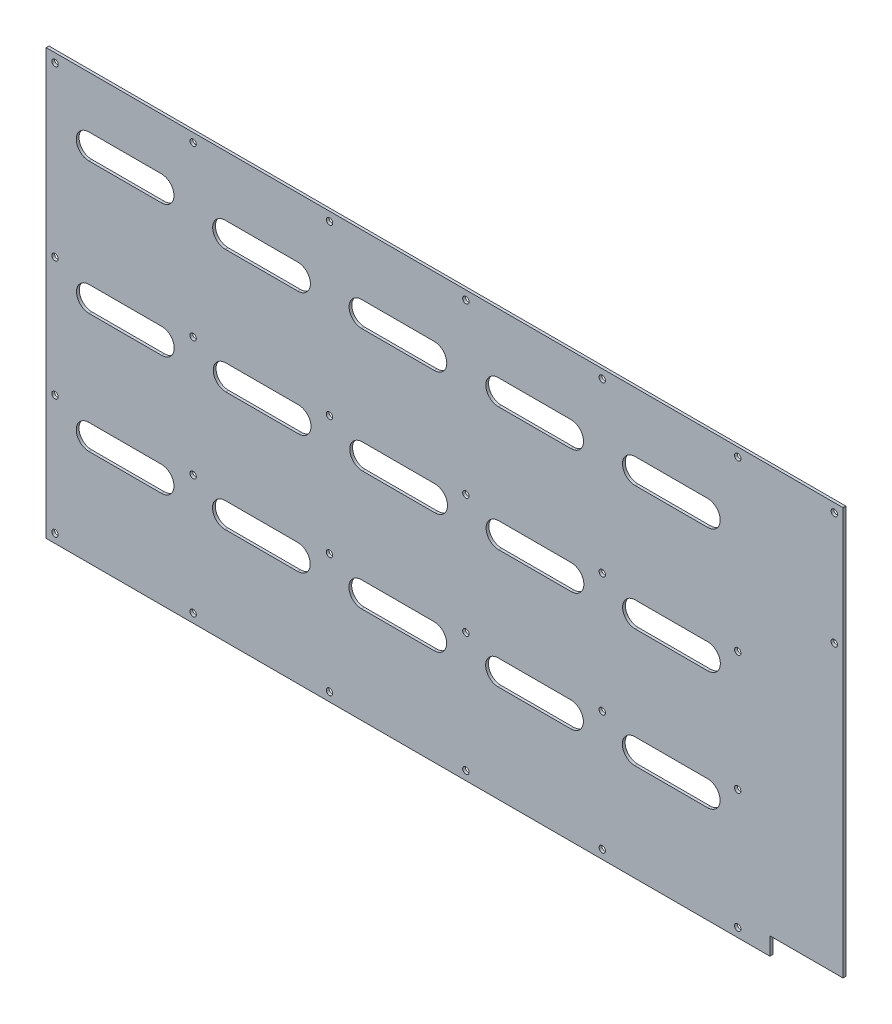
SolidWorks part; units mm, degrees
ref_plane "Front Plane" through (0, 0, 0) normal (0, 0, 1) x (1, 0, 0)
ref_plane "Top Plane" through (0, 0, 0) normal (0, 1, 0) x (1, 0, 0)
ref_plane "Right Plane" through (0, 0, 0) normal (1, 0, 0) x (0, 0, -1)
sketch "Model" plane through (0, 0, 0) normal (0, 0, 1) x (1, 0, 0)
  line L0 (0, 0) -> (415.29, 0)
  line L1 (415.29, 0) -> (415.29, 10.16)
  line L2 (415.29, 10.16) -> (457.2, 10.16)
  line L3 (457.2, 10.16) -> (457.2, 243.84)
  line L4 (457.2, 243.84) -> (0, 243.84)
  line L5 (0, 243.84) -> (0, 0)
  line L6 (24.4986, 214.1733) -> (66.1546, 214.1733)
  line L7 (66.1546, 199.7717) -> (24.4986, 199.7717)
  line L8 (102.7478, 209.4238) -> (144.4038, 209.4238)
  line L9 (144.4038, 195.0222) -> (102.7478, 195.0222)
  line L10 (180.9835, 209.1621) -> (222.6395, 209.1621)
  line L11 (222.6395, 194.7605) -> (180.9835, 194.7605)
  line L12 (259.428, 209.5421) -> (301.084, 209.5421)
  line L13 (301.084, 195.1405) -> (259.428, 195.1405)
  line L14 (337.8398, 209.595) -> (379.4958, 209.595)
  line L15 (379.4958, 195.1933) -> (337.8398, 195.1933)
  line L16 (24.6392, 138.4629) -> (66.2952, 138.4629)
  line L17 (66.2952, 124.0613) -> (24.6392, 124.0613)
  line L18 (103.0965, 138.71) -> (144.7525, 138.71)
  line L19 (144.7525, 124.3084) -> (103.0965, 124.3084)
  line L20 (181.3907, 138.6208) -> (223.0467, 138.6208)
  line L21 (223.0467, 124.2191) -> (181.3907, 124.2191)
  line L22 (259.6081, 138.5703) -> (301.2641, 138.5703)
  line L23 (301.2641, 124.1687) -> (259.6081, 124.1687)
  line L24 (337.9084, 138.3784) -> (379.5644, 138.3784)
  line L25 (379.5644, 123.9768) -> (337.9084, 123.9768)
  line L26 (24.487, 69.8646) -> (66.143, 69.8646)
  line L27 (66.143, 55.463) -> (24.487, 55.463)
  line L28 (102.6591, 70.1547) -> (144.3151, 70.1547)
  line L29 (144.3151, 55.7531) -> (102.6591, 55.7531)
  line L30 (180.8949, 69.893) -> (222.5509, 69.893)
  line L31 (222.5509, 55.4913) -> (180.8949, 55.4913)
  line L32 (259.3394, 70.2729) -> (300.9954, 70.2729)
  line L33 (300.9954, 55.8713) -> (259.3394, 55.8713)
  line L34 (337.7512, 70.3258) -> (379.4072, 70.3258)
  line L35 (379.4072, 55.9242) -> (337.7512, 55.9242)
  line L276 (452.12, 173.736) -> (452.12, 174.244)
  line L277 (451.866, 173.99) -> (452.374, 173.99)
  line L278 (452.12, 173.736) -> (452.12, 174.244)
  line L279 (451.866, 173.99) -> (452.374, 173.99)
  line L280 (452.12, 173.736) -> (452.12, 174.244)
  line L281 (451.866, 173.99) -> (452.374, 173.99)
  line L282 (452.12, 173.736) -> (452.12, 174.244)
  line L283 (451.866, 173.99) -> (452.374, 173.99)
  line L284 (452.12, 173.736) -> (452.12, 174.244)
  line L285 (451.866, 173.99) -> (452.374, 173.99)
  line L286 (452.12, 173.736) -> (452.12, 174.244)
  line L287 (451.866, 173.99) -> (452.374, 173.99)
  line L288 (452.12, 173.736) -> (452.12, 174.244)
  line L289 (451.866, 173.99) -> (452.374, 173.99)
  line L290 (452.12, 173.736) -> (452.12, 174.244)
  line L291 (451.866, 173.99) -> (452.374, 173.99)
  line L292 (452.12, 238.506) -> (452.12, 239.014)
  line L293 (451.866, 238.76) -> (452.374, 238.76)
  line L294 (452.12, 238.506) -> (452.12, 239.014)
  line L295 (451.866, 238.76) -> (452.374, 238.76)
  line L296 (452.12, 238.506) -> (452.12, 239.014)
  line L297 (451.866, 238.76) -> (452.374, 238.76)
  line L298 (452.12, 238.506) -> (452.12, 239.014)
  line L299 (451.866, 238.76) -> (452.374, 238.76)
  line L300 (452.12, 238.506) -> (452.12, 239.014)
  line L301 (451.866, 238.76) -> (452.374, 238.76)
  line L302 (452.12, 238.506) -> (452.12, 239.014)
  line L303 (451.866, 238.76) -> (452.374, 238.76)
  line L304 (452.12, 238.506) -> (452.12, 239.014)
  line L305 (451.866, 238.76) -> (452.374, 238.76)
  line L306 (452.12, 238.506) -> (452.12, 239.014)
  line L307 (451.866, 238.76) -> (452.374, 238.76)
  line L308 (5.08, 4.826) -> (5.08, 5.334)
  line L309 (4.826, 5.08) -> (5.334, 5.08)
  line L310 (5.08, 4.826) -> (5.08, 5.334)
  line L311 (4.826, 5.08) -> (5.334, 5.08)
  line L312 (5.08, 4.826) -> (5.08, 5.334)
  line L313 (4.826, 5.08) -> (5.334, 5.08)
  line L314 (5.08, 4.826) -> (5.08, 5.334)
  line L315 (4.826, 5.08) -> (5.334, 5.08)
  line L316 (5.08, 4.826) -> (5.08, 5.334)
  line L317 (4.826, 5.08) -> (5.334, 5.08)
  line L318 (5.08, 4.826) -> (5.08, 5.334)
  line L319 (4.826, 5.08) -> (5.334, 5.08)
  line L320 (5.08, 4.826) -> (5.08, 5.334)
  line L321 (4.826, 5.08) -> (5.334, 5.08)
  line L322 (5.08, 4.826) -> (5.08, 5.334)
  line L323 (4.826, 5.08) -> (5.334, 5.08)
  line L324 (5.08, 73.406) -> (5.08, 73.914)
  line L325 (4.826, 73.66) -> (5.334, 73.66)
  line L326 (5.08, 73.406) -> (5.08, 73.914)
  line L327 (4.826, 73.66) -> (5.334, 73.66)
  line L328 (5.08, 73.406) -> (5.08, 73.914)
  line L329 (4.826, 73.66) -> (5.334, 73.66)
  line L330 (5.08, 73.406) -> (5.08, 73.914)
  line L331 (4.826, 73.66) -> (5.334, 73.66)
  line L332 (5.08, 73.406) -> (5.08, 73.914)
  line L333 (4.826, 73.66) -> (5.334, 73.66)
  line L334 (5.08, 73.406) -> (5.08, 73.914)
  line L335 (4.826, 73.66) -> (5.334, 73.66)
  line L336 (5.08, 73.406) -> (5.08, 73.914)
  line L337 (4.826, 73.66) -> (5.334, 73.66)
  line L338 (5.08, 73.406) -> (5.08, 73.914)
  line L339 (4.826, 73.66) -> (5.334, 73.66)
  line L340 (5.08, 141.986) -> (5.08, 142.494)
  line L341 (4.826, 142.24) -> (5.334, 142.24)
  line L342 (5.08, 141.986) -> (5.08, 142.494)
  line L343 (4.826, 142.24) -> (5.334, 142.24)
  line L344 (5.08, 141.986) -> (5.08, 142.494)
  line L345 (4.826, 142.24) -> (5.334, 142.24)
  line L346 (5.08, 141.986) -> (5.08, 142.494)
  line L347 (4.826, 142.24) -> (5.334, 142.24)
  line L348 (5.08, 141.986) -> (5.08, 142.494)
  line L349 (4.826, 142.24) -> (5.334, 142.24)
  line L350 (5.08, 141.986) -> (5.08, 142.494)
  line L351 (4.826, 142.24) -> (5.334, 142.24)
  line L352 (5.08, 141.986) -> (5.08, 142.494)
  line L353 (4.826, 142.24) -> (5.334, 142.24)
  line L354 (5.08, 141.986) -> (5.08, 142.494)
  line L355 (4.826, 142.24) -> (5.334, 142.24)
  line L356 (5.08, 238.506) -> (5.08, 239.014)
  line L357 (4.826, 238.76) -> (5.334, 238.76)
  line L358 (5.08, 238.506) -> (5.08, 239.014)
  line L359 (4.826, 238.76) -> (5.334, 238.76)
  line L360 (5.08, 238.506) -> (5.08, 239.014)
  line L361 (4.826, 238.76) -> (5.334, 238.76)
  line L362 (5.08, 238.506) -> (5.08, 239.014)
  line L363 (4.826, 238.76) -> (5.334, 238.76)
  line L364 (5.08, 238.506) -> (5.08, 239.014)
  line L365 (4.826, 238.76) -> (5.334, 238.76)
  line L366 (5.08, 238.506) -> (5.08, 239.014)
  line L367 (4.826, 238.76) -> (5.334, 238.76)
  line L368 (5.08, 238.506) -> (5.08, 239.014)
  line L369 (4.826, 238.76) -> (5.334, 238.76)
  line L370 (5.08, 238.506) -> (5.08, 239.014)
  line L371 (4.826, 238.76) -> (5.334, 238.76)
  line L372 (84.328, 4.826) -> (84.328, 5.334)
  line L373 (84.074, 5.08) -> (84.582, 5.08)
  line L374 (84.328, 4.826) -> (84.328, 5.334)
  line L375 (84.074, 5.08) -> (84.582, 5.08)
  line L376 (84.328, 4.826) -> (84.328, 5.334)
  line L377 (84.074, 5.08) -> (84.582, 5.08)
  line L378 (84.328, 4.826) -> (84.328, 5.334)
  line L379 (84.074, 5.08) -> (84.582, 5.08)
  line L380 (84.328, 4.826) -> (84.328, 5.334)
  line L381 (84.074, 5.08) -> (84.582, 5.08)
  line L382 (84.328, 4.826) -> (84.328, 5.334)
  line L383 (84.074, 5.08) -> (84.582, 5.08)
  line L384 (84.328, 4.826) -> (84.328, 5.334)
  line L385 (84.074, 5.08) -> (84.582, 5.08)
  line L386 (84.328, 4.826) -> (84.328, 5.334)
  line L387 (84.074, 5.08) -> (84.582, 5.08)
  line L388 (84.328, 73.406) -> (84.328, 73.914)
  line L389 (84.074, 73.66) -> (84.582, 73.66)
  line L390 (84.328, 73.406) -> (84.328, 73.914)
  line L391 (84.074, 73.66) -> (84.582, 73.66)
  line L392 (84.328, 73.406) -> (84.328, 73.914)
  line L393 (84.074, 73.66) -> (84.582, 73.66)
  line L394 (84.328, 73.406) -> (84.328, 73.914)
  line L395 (84.074, 73.66) -> (84.582, 73.66)
  line L396 (84.328, 73.406) -> (84.328, 73.914)
  line L397 (84.074, 73.66) -> (84.582, 73.66)
  line L398 (84.328, 73.406) -> (84.328, 73.914)
  line L399 (84.074, 73.66) -> (84.582, 73.66)
  line L400 (84.328, 73.406) -> (84.328, 73.914)
  line L401 (84.074, 73.66) -> (84.582, 73.66)
  line L402 (84.328, 73.406) -> (84.328, 73.914)
  line L403 (84.074, 73.66) -> (84.582, 73.66)
  line L404 (84.328, 141.986) -> (84.328, 142.494)
  line L405 (84.074, 142.24) -> (84.582, 142.24)
  line L406 (84.328, 141.986) -> (84.328, 142.494)
  line L407 (84.074, 142.24) -> (84.582, 142.24)
  line L408 (84.328, 141.986) -> (84.328, 142.494)
  line L409 (84.074, 142.24) -> (84.582, 142.24)
  line L410 (84.328, 141.986) -> (84.328, 142.494)
  line L411 (84.074, 142.24) -> (84.582, 142.24)
  line L412 (84.328, 141.986) -> (84.328, 142.494)
  line L413 (84.074, 142.24) -> (84.582, 142.24)
  line L414 (84.328, 141.986) -> (84.328, 142.494)
  line L415 (84.074, 142.24) -> (84.582, 142.24)
  line L416 (84.328, 141.986) -> (84.328, 142.494)
  line L417 (84.074, 142.24) -> (84.582, 142.24)
  line L418 (84.328, 141.986) -> (84.328, 142.494)
  line L419 (84.074, 142.24) -> (84.582, 142.24)
  line L420 (84.328, 238.506) -> (84.328, 239.014)
  line L421 (84.074, 238.76) -> (84.582, 238.76)
  line L422 (84.328, 238.506) -> (84.328, 239.014)
  line L423 (84.074, 238.76) -> (84.582, 238.76)
  line L424 (84.328, 238.506) -> (84.328, 239.014)
  line L425 (84.074, 238.76) -> (84.582, 238.76)
  line L426 (84.328, 238.506) -> (84.328, 239.014)
  line L427 (84.074, 238.76) -> (84.582, 238.76)
  line L428 (84.328, 238.506) -> (84.328, 239.014)
  line L429 (84.074, 238.76) -> (84.582, 238.76)
  line L430 (84.328, 238.506) -> (84.328, 239.014)
  line L431 (84.074, 238.76) -> (84.582, 238.76)
  line L432 (84.328, 238.506) -> (84.328, 239.014)
  line L433 (84.074, 238.76) -> (84.582, 238.76)
  line L434 (84.328, 238.506) -> (84.328, 239.014)
  line L435 (84.074, 238.76) -> (84.582, 238.76)
  line L436 (162.56, 4.826) -> (162.56, 5.334)
  line L437 (162.306, 5.08) -> (162.814, 5.08)
  line L438 (162.56, 4.826) -> (162.56, 5.334)
  line L439 (162.306, 5.08) -> (162.814, 5.08)
  line L440 (162.56, 4.826) -> (162.56, 5.334)
  line L441 (162.306, 5.08) -> (162.814, 5.08)
  line L442 (162.56, 4.826) -> (162.56, 5.334)
  line L443 (162.306, 5.08) -> (162.814, 5.08)
  line L444 (162.56, 4.826) -> (162.56, 5.334)
  line L445 (162.306, 5.08) -> (162.814, 5.08)
  line L446 (162.56, 4.826) -> (162.56, 5.334)
  line L447 (162.306, 5.08) -> (162.814, 5.08)
  line L448 (162.56, 4.826) -> (162.56, 5.334)
  line L449 (162.306, 5.08) -> (162.814, 5.08)
  line L450 (162.56, 4.826) -> (162.56, 5.334)
  line L451 (162.306, 5.08) -> (162.814, 5.08)
  line L452 (162.56, 73.406) -> (162.56, 73.914)
  line L453 (162.306, 73.66) -> (162.814, 73.66)
  line L454 (162.56, 73.406) -> (162.56, 73.914)
  line L455 (162.306, 73.66) -> (162.814, 73.66)
  line L456 (162.56, 73.406) -> (162.56, 73.914)
  line L457 (162.306, 73.66) -> (162.814, 73.66)
  line L458 (162.56, 73.406) -> (162.56, 73.914)
  line L459 (162.306, 73.66) -> (162.814, 73.66)
  line L460 (162.56, 73.406) -> (162.56, 73.914)
  line L461 (162.306, 73.66) -> (162.814, 73.66)
  line L462 (162.56, 73.406) -> (162.56, 73.914)
  line L463 (162.306, 73.66) -> (162.814, 73.66)
  line L464 (162.56, 73.406) -> (162.56, 73.914)
  line L465 (162.306, 73.66) -> (162.814, 73.66)
  line L466 (162.56, 73.406) -> (162.56, 73.914)
  line L467 (162.306, 73.66) -> (162.814, 73.66)
  line L468 (162.56, 141.986) -> (162.56, 142.494)
  line L469 (162.306, 142.24) -> (162.814, 142.24)
  line L470 (162.56, 141.986) -> (162.56, 142.494)
  line L471 (162.306, 142.24) -> (162.814, 142.24)
  line L472 (162.56, 141.986) -> (162.56, 142.494)
  line L473 (162.306, 142.24) -> (162.814, 142.24)
  line L474 (162.56, 141.986) -> (162.56, 142.494)
  line L475 (162.306, 142.24) -> (162.814, 142.24)
  line L476 (162.56, 141.986) -> (162.56, 142.494)
  line L477 (162.306, 142.24) -> (162.814, 142.24)
  line L478 (162.56, 141.986) -> (162.56, 142.494)
  line L479 (162.306, 142.24) -> (162.814, 142.24)
  line L480 (162.56, 141.986) -> (162.56, 142.494)
  line L481 (162.306, 142.24) -> (162.814, 142.24)
  line L482 (162.56, 141.986) -> (162.56, 142.494)
  line L483 (162.306, 142.24) -> (162.814, 142.24)
  line L484 (162.56, 238.506) -> (162.56, 239.014)
  line L485 (162.306, 238.76) -> (162.814, 238.76)
  line L486 (162.56, 238.506) -> (162.56, 239.014)
  line L487 (162.306, 238.76) -> (162.814, 238.76)
  line L488 (162.56, 238.506) -> (162.56, 239.014)
  line L489 (162.306, 238.76) -> (162.814, 238.76)
  line L490 (162.56, 238.506) -> (162.56, 239.014)
  line L491 (162.306, 238.76) -> (162.814, 238.76)
  line L492 (162.56, 238.506) -> (162.56, 239.014)
  line L493 (162.306, 238.76) -> (162.814, 238.76)
  line L494 (162.56, 238.506) -> (162.56, 239.014)
  line L495 (162.306, 238.76) -> (162.814, 238.76)
  line L496 (162.56, 238.506) -> (162.56, 239.014)
  line L497 (162.306, 238.76) -> (162.814, 238.76)
  line L498 (162.56, 238.506) -> (162.56, 239.014)
  line L499 (162.306, 238.76) -> (162.814, 238.76)
  line L500 (240.7699, 4.827) -> (240.8141, 5.333)
  line L501 (240.539, 5.1021) -> (241.045, 5.0579)
  line L502 (240.7699, 4.827) -> (240.8141, 5.333)
  line L503 (240.539, 5.1021) -> (241.045, 5.0579)
  line L504 (240.7699, 4.827) -> (240.8141, 5.333)
  line L505 (240.539, 5.1021) -> (241.045, 5.0579)
  line L506 (240.7699, 4.827) -> (240.8141, 5.333)
  line L507 (240.539, 5.1021) -> (241.045, 5.0579)
  line L508 (240.7699, 4.827) -> (240.8141, 5.333)
  line L509 (240.539, 5.1021) -> (241.045, 5.0579)
  line L510 (240.7699, 4.827) -> (240.8141, 5.333)
  line L511 (240.539, 5.1021) -> (241.045, 5.0579)
  line L512 (240.7699, 4.827) -> (240.8141, 5.333)
  line L513 (240.539, 5.1021) -> (241.045, 5.0579)
  line L514 (240.7699, 4.827) -> (240.8141, 5.333)
  line L515 (240.539, 5.1021) -> (241.045, 5.0579)
  line L516 (240.792, 73.406) -> (240.792, 73.914)
  line L517 (240.538, 73.66) -> (241.046, 73.66)
  line L518 (240.792, 73.406) -> (240.792, 73.914)
  line L519 (240.538, 73.66) -> (241.046, 73.66)
  line L520 (240.792, 73.406) -> (240.792, 73.914)
  line L521 (240.538, 73.66) -> (241.046, 73.66)
  line L522 (240.792, 73.406) -> (240.792, 73.914)
  line L523 (240.538, 73.66) -> (241.046, 73.66)
  line L524 (240.792, 73.406) -> (240.792, 73.914)
  line L525 (240.538, 73.66) -> (241.046, 73.66)
  line L526 (240.792, 73.406) -> (240.792, 73.914)
  line L527 (240.538, 73.66) -> (241.046, 73.66)
  line L528 (240.792, 73.406) -> (240.792, 73.914)
  line L529 (240.538, 73.66) -> (241.046, 73.66)
  line L530 (240.792, 73.406) -> (240.792, 73.914)
  line L531 (240.538, 73.66) -> (241.046, 73.66)
  line L532 (240.792, 141.986) -> (240.792, 142.494)
  line L533 (240.538, 142.24) -> (241.046, 142.24)
  line L534 (240.792, 141.986) -> (240.792, 142.494)
  line L535 (240.538, 142.24) -> (241.046, 142.24)
  line L536 (240.792, 141.986) -> (240.792, 142.494)
  line L537 (240.538, 142.24) -> (241.046, 142.24)
  line L538 (240.792, 141.986) -> (240.792, 142.494)
  line L539 (240.538, 142.24) -> (241.046, 142.24)
  line L540 (240.792, 141.986) -> (240.792, 142.494)
  line L541 (240.538, 142.24) -> (241.046, 142.24)
  line L542 (240.792, 141.986) -> (240.792, 142.494)
  line L543 (240.538, 142.24) -> (241.046, 142.24)
  line L544 (240.792, 141.986) -> (240.792, 142.494)
  line L545 (240.538, 142.24) -> (241.046, 142.24)
  line L546 (240.792, 141.986) -> (240.792, 142.494)
  line L547 (240.538, 142.24) -> (241.046, 142.24)
  line L548 (240.792, 238.506) -> (240.792, 239.014)
  line L549 (240.538, 238.76) -> (241.046, 238.76)
  line L550 (240.792, 238.506) -> (240.792, 239.014)
  line L551 (240.538, 238.76) -> (241.046, 238.76)
  line L552 (240.792, 238.506) -> (240.792, 239.014)
  line L553 (240.538, 238.76) -> (241.046, 238.76)
  line L554 (240.792, 238.506) -> (240.792, 239.014)
  line L555 (240.538, 238.76) -> (241.046, 238.76)
  line L556 (240.792, 238.506) -> (240.792, 239.014)
  line L557 (240.538, 238.76) -> (241.046, 238.76)
  line L558 (240.792, 238.506) -> (240.792, 239.014)
  line L559 (240.538, 238.76) -> (241.046, 238.76)
  line L560 (240.792, 238.506) -> (240.792, 239.014)
  line L561 (240.538, 238.76) -> (241.046, 238.76)
  line L562 (240.792, 238.506) -> (240.792, 239.014)
  line L563 (240.538, 238.76) -> (241.046, 238.76)
  line L564 (319.024, 4.826) -> (319.024, 5.334)
  line L565 (318.77, 5.08) -> (319.278, 5.08)
  line L566 (319.024, 4.826) -> (319.024, 5.334)
  line L567 (318.77, 5.08) -> (319.278, 5.08)
  line L568 (319.024, 4.826) -> (319.024, 5.334)
  line L569 (318.77, 5.08) -> (319.278, 5.08)
  line L570 (319.024, 4.826) -> (319.024, 5.334)
  line L571 (318.77, 5.08) -> (319.278, 5.08)
  line L572 (319.024, 4.826) -> (319.024, 5.334)
  line L573 (318.77, 5.08) -> (319.278, 5.08)
  line L574 (319.024, 4.826) -> (319.024, 5.334)
  line L575 (318.77, 5.08) -> (319.278, 5.08)
  line L576 (319.024, 4.826) -> (319.024, 5.334)
  line L577 (318.77, 5.08) -> (319.278, 5.08)
  line L578 (319.024, 4.826) -> (319.024, 5.334)
  line L579 (318.77, 5.08) -> (319.278, 5.08)
  line L580 (319.024, 73.406) -> (319.024, 73.914)
  line L581 (318.77, 73.66) -> (319.278, 73.66)
  line L582 (319.024, 73.406) -> (319.024, 73.914)
  line L583 (318.77, 73.66) -> (319.278, 73.66)
  line L584 (319.024, 73.406) -> (319.024, 73.914)
  line L585 (318.77, 73.66) -> (319.278, 73.66)
  line L586 (319.024, 73.406) -> (319.024, 73.914)
  line L587 (318.77, 73.66) -> (319.278, 73.66)
  line L588 (319.024, 73.406) -> (319.024, 73.914)
  line L589 (318.77, 73.66) -> (319.278, 73.66)
  line L590 (319.024, 73.406) -> (319.024, 73.914)
  line L591 (318.77, 73.66) -> (319.278, 73.66)
  line L592 (319.024, 73.406) -> (319.024, 73.914)
  line L593 (318.77, 73.66) -> (319.278, 73.66)
  line L594 (319.024, 73.406) -> (319.024, 73.914)
  line L595 (318.77, 73.66) -> (319.278, 73.66)
  line L596 (319.024, 141.986) -> (319.024, 142.494)
  line L597 (318.77, 142.24) -> (319.278, 142.24)
  line L598 (319.024, 141.986) -> (319.024, 142.494)
  line L599 (318.77, 142.24) -> (319.278, 142.24)
  line L600 (319.024, 141.986) -> (319.024, 142.494)
  line L601 (318.77, 142.24) -> (319.278, 142.24)
  line L602 (319.024, 141.986) -> (319.024, 142.494)
  line L603 (318.77, 142.24) -> (319.278, 142.24)
  line L604 (319.024, 141.986) -> (319.024, 142.494)
  line L605 (318.77, 142.24) -> (319.278, 142.24)
  line L606 (319.024, 141.986) -> (319.024, 142.494)
  line L607 (318.77, 142.24) -> (319.278, 142.24)
  line L608 (319.024, 141.986) -> (319.024, 142.494)
  line L609 (318.77, 142.24) -> (319.278, 142.24)
  line L610 (319.024, 141.986) -> (319.024, 142.494)
  line L611 (318.77, 142.24) -> (319.278, 142.24)
  line L612 (319.024, 238.506) -> (319.024, 239.014)
  line L613 (318.77, 238.76) -> (319.278, 238.76)
  line L614 (319.024, 238.506) -> (319.024, 239.014)
  line L615 (318.77, 238.76) -> (319.278, 238.76)
  line L616 (319.024, 238.506) -> (319.024, 239.014)
  line L617 (318.77, 238.76) -> (319.278, 238.76)
  line L618 (319.024, 238.506) -> (319.024, 239.014)
  line L619 (318.77, 238.76) -> (319.278, 238.76)
  line L620 (319.024, 238.506) -> (319.024, 239.014)
  line L621 (318.77, 238.76) -> (319.278, 238.76)
  line L622 (319.024, 238.506) -> (319.024, 239.014)
  line L623 (318.77, 238.76) -> (319.278, 238.76)
  line L624 (319.024, 238.506) -> (319.024, 239.014)
  line L625 (318.77, 238.76) -> (319.278, 238.76)
  line L626 (319.024, 238.506) -> (319.024, 239.014)
  line L627 (318.77, 238.76) -> (319.278, 238.76)
  line L628 (396.748, 4.826) -> (396.748, 5.334)
  line L629 (396.494, 5.08) -> (397.002, 5.08)
  line L630 (396.748, 4.826) -> (396.748, 5.334)
  line L631 (396.494, 5.08) -> (397.002, 5.08)
  line L632 (396.748, 4.826) -> (396.748, 5.334)
  line L633 (396.494, 5.08) -> (397.002, 5.08)
  line L634 (396.748, 4.826) -> (396.748, 5.334)
  line L635 (396.494, 5.08) -> (397.002, 5.08)
  line L636 (396.748, 4.826) -> (396.748, 5.334)
  line L637 (396.494, 5.08) -> (397.002, 5.08)
  line L638 (396.748, 4.826) -> (396.748, 5.334)
  line L639 (396.494, 5.08) -> (397.002, 5.08)
  line L640 (396.748, 4.826) -> (396.748, 5.334)
  line L641 (396.494, 5.08) -> (397.002, 5.08)
  line L642 (396.748, 4.826) -> (396.748, 5.334)
  line L643 (396.494, 5.08) -> (397.002, 5.08)
  line L644 (396.748, 73.406) -> (396.748, 73.914)
  line L645 (396.494, 73.66) -> (397.002, 73.66)
  line L646 (396.748, 73.406) -> (396.748, 73.914)
  line L647 (396.494, 73.66) -> (397.002, 73.66)
  line L648 (396.748, 73.406) -> (396.748, 73.914)
  line L649 (396.494, 73.66) -> (397.002, 73.66)
  line L650 (396.748, 73.406) -> (396.748, 73.914)
  line L651 (396.494, 73.66) -> (397.002, 73.66)
  line L652 (396.748, 73.406) -> (396.748, 73.914)
  line L653 (396.494, 73.66) -> (397.002, 73.66)
  line L654 (396.748, 73.406) -> (396.748, 73.914)
  line L655 (396.494, 73.66) -> (397.002, 73.66)
  line L656 (396.748, 73.406) -> (396.748, 73.914)
  line L657 (396.494, 73.66) -> (397.002, 73.66)
  line L658 (396.748, 73.406) -> (396.748, 73.914)
  line L659 (396.494, 73.66) -> (397.002, 73.66)
  line L660 (396.748, 141.986) -> (396.748, 142.494)
  line L661 (396.494, 142.24) -> (397.002, 142.24)
  line L662 (396.748, 141.986) -> (396.748, 142.494)
  line L663 (396.494, 142.24) -> (397.002, 142.24)
  line L664 (396.748, 141.986) -> (396.748, 142.494)
  line L665 (396.494, 142.24) -> (397.002, 142.24)
  line L666 (396.748, 141.986) -> (396.748, 142.494)
  line L667 (396.494, 142.24) -> (397.002, 142.24)
  line L668 (396.748, 141.986) -> (396.748, 142.494)
  line L669 (396.494, 142.24) -> (397.002, 142.24)
  line L670 (396.748, 141.986) -> (396.748, 142.494)
  line L671 (396.494, 142.24) -> (397.002, 142.24)
  line L672 (396.748, 141.986) -> (396.748, 142.494)
  line L673 (396.494, 142.24) -> (397.002, 142.24)
  line L674 (396.748, 141.986) -> (396.748, 142.494)
  line L675 (396.494, 142.24) -> (397.002, 142.24)
  line L676 (396.748, 238.506) -> (396.748, 239.014)
  line L677 (396.494, 238.76) -> (397.002, 238.76)
  line L678 (396.748, 238.506) -> (396.748, 239.014)
  line L679 (396.494, 238.76) -> (397.002, 238.76)
  line L680 (396.748, 238.506) -> (396.748, 239.014)
  line L681 (396.494, 238.76) -> (397.002, 238.76)
  line L682 (396.748, 238.506) -> (396.748, 239.014)
  line L683 (396.494, 238.76) -> (397.002, 238.76)
  line L684 (396.748, 238.506) -> (396.748, 239.014)
  line L685 (396.494, 238.76) -> (397.002, 238.76)
  line L686 (396.748, 238.506) -> (396.748, 239.014)
  line L687 (396.494, 238.76) -> (397.002, 238.76)
  line L688 (396.748, 238.506) -> (396.748, 239.014)
  line L689 (396.494, 238.76) -> (397.002, 238.76)
  line L690 (396.748, 238.506) -> (396.748, 239.014)
  line L691 (396.494, 238.76) -> (397.002, 238.76)
  circle A0 centre (0, 0) radius 0.0635
  circle A1 centre (415.29, 0) radius 0.0635
  circle A2 centre (415.29, 10.16) radius 0.0635
  circle A3 centre (457.2, 10.16) radius 0.0635
  circle A4 centre (457.2, 243.84) radius 0.0635
  circle A5 centre (0, 243.84) radius 0.0635
  arc A6 (66.1546, 199.7717) -> (66.1546, 214.1733) centre (66.1546, 206.9725) ccw
  arc A7 (24.4986, 214.1733) -> (24.4986, 199.7717) centre (24.4986, 206.9725) ccw
  circle A8 centre (24.4986, 214.1733) radius 0.0635
  circle A9 centre (66.1546, 214.1733) radius 0.0635
  arc A10 (144.4038, 195.0222) -> (144.4038, 209.4238) centre (144.4038, 202.223) ccw
  arc A11 (102.7478, 209.4238) -> (102.7478, 195.0222) centre (102.7478, 202.223) ccw
  circle A12 centre (102.7478, 209.4238) radius 0.0635
  circle A13 centre (144.4038, 209.4238) radius 0.0635
  arc A14 (222.6395, 194.7605) -> (222.6395, 209.1621) centre (222.6395, 201.9613) ccw
  arc A15 (180.9835, 209.1621) -> (180.9835, 194.7605) centre (180.9835, 201.9613) ccw
  circle A16 centre (180.9835, 209.1621) radius 0.0635
  circle A17 centre (222.6395, 209.1621) radius 0.0635
  arc A18 (301.084, 195.1405) -> (301.084, 209.5421) centre (301.084, 202.3413) ccw
  arc A19 (259.428, 209.5421) -> (259.428, 195.1405) centre (259.428, 202.3413) ccw
  circle A20 centre (259.428, 209.5421) radius 0.0635
  circle A21 centre (301.084, 209.5421) radius 0.0635
  arc A22 (379.4958, 195.1933) -> (379.4958, 209.595) centre (379.4958, 202.3942) ccw
  arc A23 (337.8398, 209.595) -> (337.8398, 195.1933) centre (337.8398, 202.3942) ccw
  circle A24 centre (337.8398, 209.595) radius 0.0635
  circle A25 centre (379.4958, 209.595) radius 0.0635
  arc A26 (66.2952, 124.0613) -> (66.2952, 138.4629) centre (66.2952, 131.2621) ccw
  arc A27 (24.6392, 138.4629) -> (24.6392, 124.0613) centre (24.6392, 131.2621) ccw
  circle A28 centre (24.6392, 138.4629) radius 0.0635
  circle A29 centre (66.2952, 138.4629) radius 0.0635
  arc A30 (144.7525, 124.3084) -> (144.7525, 138.71) centre (144.7525, 131.5092) ccw
  arc A31 (103.0965, 138.71) -> (103.0965, 124.3084) centre (103.0965, 131.5092) ccw
  circle A32 centre (103.0965, 138.71) radius 0.0635
  circle A33 centre (144.7525, 138.71) radius 0.0635
  arc A34 (223.0467, 124.2191) -> (223.0467, 138.6208) centre (223.0467, 131.42) ccw
  arc A35 (181.3907, 138.6208) -> (181.3907, 124.2191) centre (181.3907, 131.42) ccw
  circle A36 centre (181.3907, 138.6208) radius 0.0635
  circle A37 centre (223.0467, 138.6208) radius 0.0635
  arc A38 (301.2641, 124.1687) -> (301.2641, 138.5703) centre (301.2641, 131.3695) ccw
  arc A39 (259.6081, 138.5703) -> (259.6081, 124.1687) centre (259.6081, 131.3695) ccw
  circle A40 centre (259.6081, 138.5703) radius 0.0635
  circle A41 centre (301.2641, 138.5703) radius 0.0635
  arc A42 (379.5644, 123.9768) -> (379.5644, 138.3784) centre (379.5644, 131.1776) ccw
  arc A43 (337.9084, 138.3784) -> (337.9084, 123.9768) centre (337.9084, 131.1776) ccw
  circle A44 centre (337.9084, 138.3784) radius 0.0635
  circle A45 centre (379.5644, 138.3784) radius 0.0635
  arc A46 (66.143, 55.463) -> (66.143, 69.8646) centre (66.143, 62.6638) ccw
  arc A47 (24.487, 69.8646) -> (24.487, 55.463) centre (24.487, 62.6638) ccw
  circle A48 centre (24.487, 69.8646) radius 0.0635
  circle A49 centre (66.143, 69.8646) radius 0.0635
  arc A50 (144.3151, 55.7531) -> (144.3151, 70.1547) centre (144.3151, 62.9539) ccw
  arc A51 (102.6591, 70.1547) -> (102.6591, 55.7531) centre (102.6591, 62.9539) ccw
  circle A52 centre (102.6591, 70.1547) radius 0.0635
  circle A53 centre (144.3151, 70.1547) radius 0.0635
  arc A54 (222.5509, 55.4913) -> (222.5509, 69.893) centre (222.5509, 62.6921) ccw
  arc A55 (180.8949, 69.893) -> (180.8949, 55.4913) centre (180.8949, 62.6921) ccw
  circle A56 centre (180.8949, 69.893) radius 0.0635
  circle A57 centre (222.5509, 69.893) radius 0.0635
  arc A58 (300.9954, 55.8713) -> (300.9954, 70.2729) centre (300.9954, 63.0721) ccw
  arc A59 (259.3394, 70.2729) -> (259.3394, 55.8713) centre (259.3394, 63.0721) ccw
  circle A60 centre (259.3394, 70.2729) radius 0.0635
  circle A61 centre (300.9954, 70.2729) radius 0.0635
  arc A62 (379.4072, 55.9242) -> (379.4072, 70.3258) centre (379.4072, 63.125) ccw
  arc A63 (337.7512, 70.3258) -> (337.7512, 55.9242) centre (337.7512, 63.125) ccw
  circle A64 centre (337.7512, 70.3258) radius 0.0635
  circle A65 centre (379.4072, 70.3258) radius 0.0635
  circle A66 centre (5.08, 238.76) radius 1.8288
  circle A67 centre (84.328, 238.76) radius 1.8288
  circle A68 centre (162.56, 238.76) radius 1.8288
  circle A69 centre (240.792, 238.76) radius 1.8288
  circle A70 centre (319.024, 238.76) radius 1.8288
  circle A71 centre (396.748, 238.76) radius 1.8288
  circle A72 centre (452.12, 238.76) radius 1.8288
  circle A73 centre (452.12, 173.99) radius 1.8288
  circle A74 centre (396.748, 142.24) radius 1.8288
  circle A75 centre (319.024, 142.24) radius 1.8288
  circle A76 centre (240.792, 142.24) radius 1.8288
  circle A77 centre (162.56, 142.24) radius 1.8288
  circle A78 centre (84.328, 142.24) radius 1.8288
  circle A79 centre (5.08, 142.24) radius 1.8288
  circle A80 centre (5.08, 73.66) radius 1.8288
  circle A81 centre (84.328, 73.66) radius 1.8288
  circle A82 centre (162.56, 73.66) radius 1.8288
  circle A83 centre (240.792, 73.66) radius 1.8288
  circle A84 centre (319.024, 73.66) radius 1.8288
  circle A85 centre (396.748, 73.66) radius 1.8288
  circle A86 centre (396.748, 5.08) radius 1.8288
  circle A87 centre (319.024, 5.08) radius 1.8288
  circle A88 centre (240.792, 5.08) radius 1.8288
  circle A89 centre (162.56, 5.08) radius 1.8288
  circle A90 centre (84.328, 5.08) radius 1.8288
  circle A91 centre (5.08, 5.08) radius 1.8288
extrude "Boss-Extrude2" add sketch "Model" along normal blind 1.5875 contours A5 L5 A0 L0 A1 L1 A2 L2 A3 L3 A4 L4 A91 A90 A89 A88 A87 A86 A85 A84 A83 A82 A81 A80 A79 A78 A77 A76 A75 A74 A73
